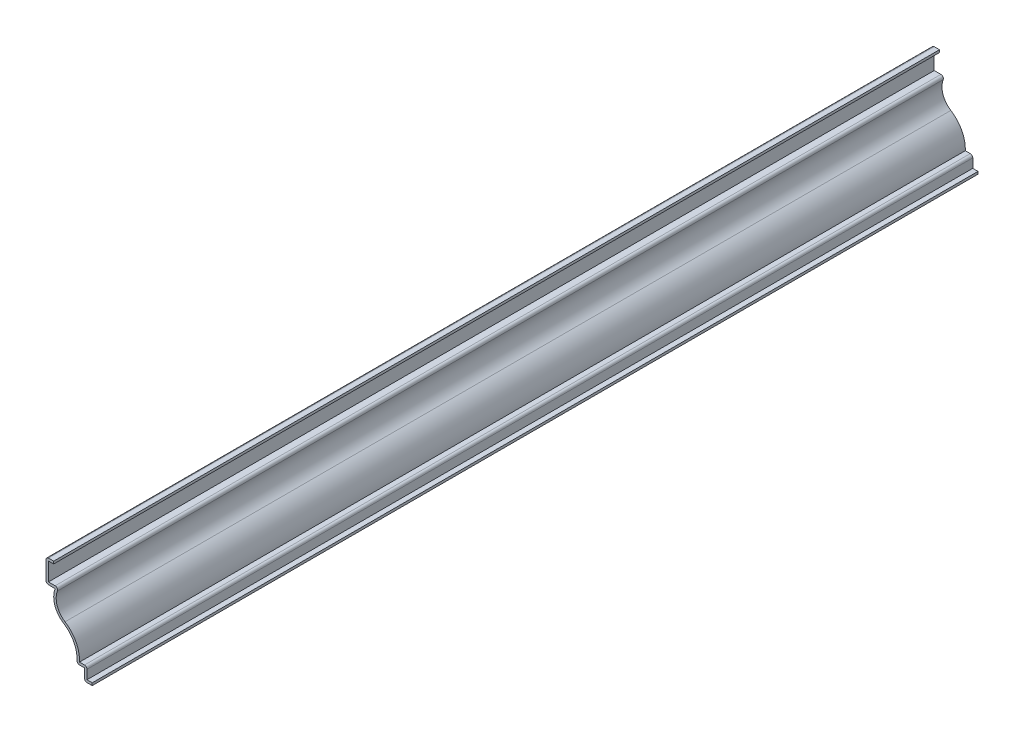
SolidWorks part; units mm, degrees
ref_plane "Front Plane" through (0, 0, 0) normal (0, 0, 1) x (1, 0, 0)
ref_plane "Top Plane" through (0, 0, 0) normal (0, 1, 0) x (1, 0, 0)
ref_plane "Right Plane" through (0, 0, 0) normal (1, 0, 0) x (0, 0, -1)
sketch "Sketch1" plane through (0, 0, 0) normal (0, 0, 1) x (1, 0, 0)
  line L0 (0, 0) -> (-3.175, 0)
  line L1 (-3.175, 0) -> (-3.175, 4.7625)
  line L2 (-3.175, 4.7625) -> (-6.35, 4.7625)
  line L3 (-15.2861, 26.9875) -> (-19.05, 26.9875)
  line L4 (-19.05, 26.9875) -> (-19.05, 36.5125)
  line L5 (-19.05, 36.5125) -> (-15.875, 36.5125)
  arc A0 (-6.35, 4.7625) -> (-11.7441, 16.3236) centre (-18.034, 6.35) ccw
  arc A1 (-11.7441, 16.3236) -> (-15.2861, 26.9875) centre (-7.0213, 23.8125) cw
  point P9 (0, 0)
  point P13 (-12.6433, 18.0728)
  point P14 (-12.1438, 18.6972)
  point P15 (-12.2012, 18.7572)
  dimension "D1" = 36.5125
  dimension "D2" = 3.175
  dimension "D3" = 9.525
  dimension "D4" = 22.225
  dimension "D5" = 3.175
  dimension "D6" = 3.175
  dimension "D7" = 19.05
  dimension "D8" = 9.525
  dimension "D9" = 1.016
  dimension "D10" = 3.175
  dimension "D11" = 1.5875
extrude "Extrude-Thin1" add sketch "Sketch1" against normal blind 365.125 thin
fillet "Fillet1" radius 1.016 6 edges at (-3.175, 0, -182.5625) (-6.35, 4.7625, -182.5625) (-19.05, 26.9875, -182.5625) (-2.159, 5.7785, -182.5625) (-13.6444, 28.0035, -182.5625) (-19.05, 36.5125, -182.5625)
